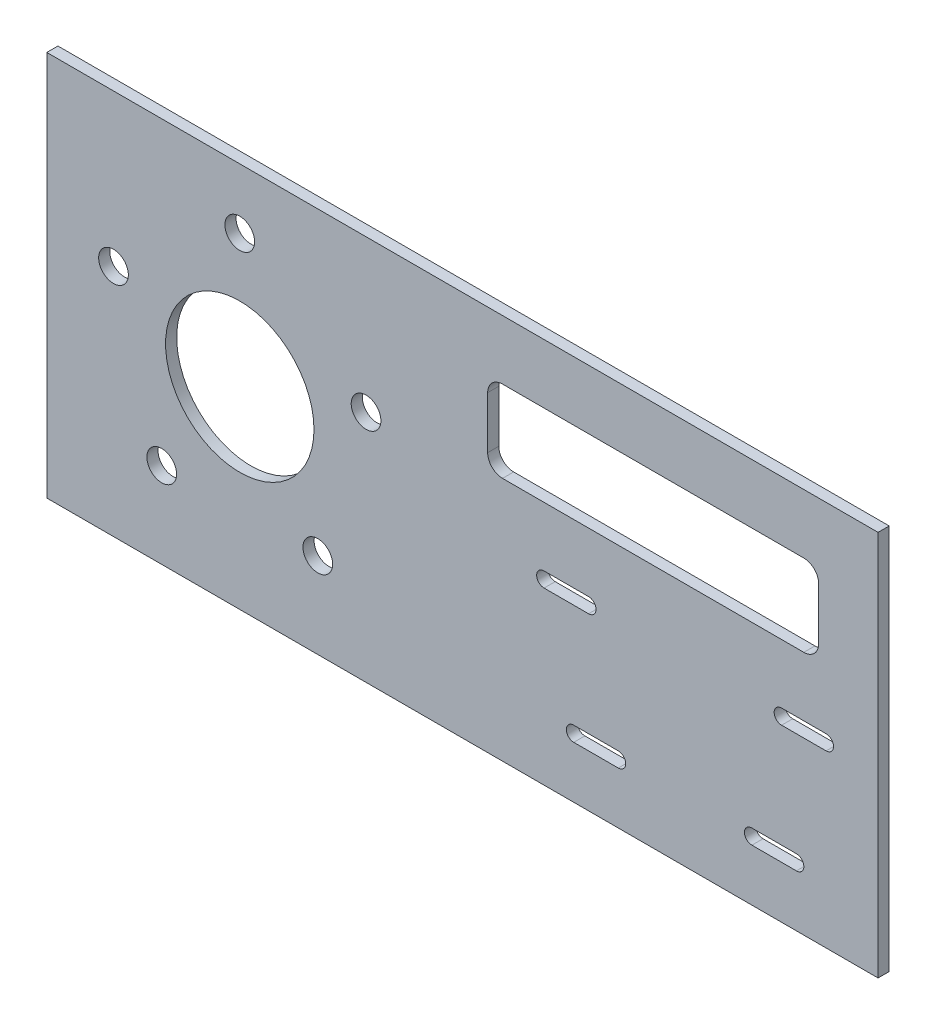
SolidWorks part; units mm, degrees
material "ASTM A36 Steel"
ref_plane "Front Plane" through (0, 0, 0) normal (0, 0, 1) x (1, 0, 0)
ref_plane "Top Plane" through (0, 0, 0) normal (0, 1, 0) x (1, 0, 0)
ref_plane "Right Plane" through (0, 0, 0) normal (1, 0, 0) x (0, 0, -1)
ref_plane "Plane1" through (190.5, 0, 0) normal (1, 0, 0) x (0, 0, -1)
sketch "Sketch1" plane through (0, 0, 0) normal (0, 0, 1) x (1, 0, 0)
  circle A2 centre (0, 0) radius 80.645
  circle A9 centre (-33.3856, -45.9513) radius 6.35
  circle A10 centre (33.3856, -45.9513) radius 6.35
  circle A11 centre (54.019, 17.5518) radius 6.35
  circle A12 centre (0, 56.7989) radius 6.35
  circle A13 centre (-54.019, 17.5518) radius 6.35
sketch "Sketch2" plane through (0, 0, 0) normal (0, 0, 1) x (1, 0, 0)
  line L0 (2.6194, 0) -> (-2.6194, 0) construction
  line L1 (273.05, -82.55) -> (-82.55, -82.55)
  line L2 (273.05, -82.55) -> (273.05, 82.55)
  line L3 (273.05, 82.55) -> (-82.55, 82.55)
  line L4 (-82.55, -82.55) -> (-82.55, 82.55)
  line L5 (273.05, -82.55) -> (-82.55, 82.55) construction
  line L6 (273.05, 82.55) -> (-82.55, -82.55) construction
  line L7 (0, -2.6194) -> (0, 2.6194) construction
  circle A0 centre (0, 0) radius 31.75
  circle A1 centre (-54.019, 17.5518) radius 6.35 construction
  circle A2 centre (0, 56.7989) radius 6.35 construction
  circle A3 centre (54.019, 17.5518) radius 6.35 construction
  circle A4 centre (33.3856, -45.9513) radius 6.35 construction
  circle A5 centre (-33.3856, -45.9513) radius 6.35 construction
  circle A6 centre (-54.019, 17.5518) radius 6.35
  circle A7 centre (0, 56.7989) radius 6.35
  circle A8 centre (54.019, 17.5518) radius 6.35
  circle A9 centre (33.3856, -45.9513) radius 6.35
  circle A10 centre (-33.3856, -45.9513) radius 6.35
  point P18 (95.25, 0)
  dimension "D1" = 63.5
  dimension "D2" = 165.1
  dimension "D3" = 82.55
  dimension "D4" = 355.6
extrude "Boss-Extrude1" add sketch "Sketch2" along normal blind 4.7625
sketch "Sketch3" plane through (0, 0, 4.7625) normal (0, 0, 1) x (1, 0, 0)
  line L0 (190.5, -2.6194) -> (190.5, 2.6194) construction
  line L1 (139.7, -6.35) -> (241.3, -6.35) construction
  line L2 (190.5, -6.35) -> (190.5, -57.15) construction
  line L3 (152.4, -57.15) -> (228.6, -57.15) construction
  line L4 (149.225, -6.35) -> (130.175, -6.35) construction
  line L5 (139.7, -6.35) -> (228.6, -57.15) construction
  line L6 (152.4, -57.15) -> (241.3, -6.35) construction
  line L7 (149.225, -9.525) -> (130.175, -9.525)
  line L8 (149.225, -3.175) -> (130.175, -3.175)
  line L9 (250.825, -6.35) -> (231.775, -6.35) construction
  line L10 (250.825, -9.525) -> (231.775, -9.525)
  line L11 (250.825, -3.175) -> (231.775, -3.175)
  line L12 (238.125, -57.15) -> (219.075, -57.15) construction
  line L13 (238.125, -60.325) -> (219.075, -60.325)
  line L14 (238.125, -53.975) -> (219.075, -53.975)
  line L15 (142.875, -57.15) -> (161.925, -57.15) construction
  line L16 (142.875, -53.975) -> (161.925, -53.975)
  line L17 (142.875, -60.325) -> (161.925, -60.325)
  line L18 (273.05, 82.55) -> (-82.55, 82.55) construction
  arc A0 (149.225, -9.525) -> (149.225, -3.175) centre (149.225, -6.35) ccw
  arc A1 (130.175, -3.175) -> (130.175, -9.525) centre (130.175, -6.35) ccw
  arc A2 (250.825, -9.525) -> (250.825, -3.175) centre (250.825, -6.35) ccw
  arc A3 (231.775, -3.175) -> (231.775, -9.525) centre (231.775, -6.35) ccw
  arc A4 (238.125, -60.325) -> (238.125, -53.975) centre (238.125, -57.15) ccw
  arc A5 (219.075, -53.975) -> (219.075, -60.325) centre (219.075, -57.15) ccw
  arc A6 (142.875, -53.975) -> (142.875, -60.325) centre (142.875, -57.15) ccw
  arc A7 (161.925, -60.325) -> (161.925, -53.975) centre (161.925, -57.15) ccw
  point P0 (190.5, -35.3786)
  point P11 (139.7, -6.35)
  point P18 (241.3, -6.35)
  point P23 (228.6, -57.15)
  point P30 (152.4, -57.15)
  dimension "D1" = 50.8
  dimension "D2" = 101.6
  dimension "D3" = 76.2
  dimension "D4" = 88.9
  dimension "D5" = 19.05
  dimension "D6" = 6.35
extrude "Cut-Extrude1" cut sketch "Sketch3" against normal through all
ref_plane "Plane2" through (0, -6.35, 0) normal (0, 1, 0) x (-1, 0, 0)
sketch "Sketch4" plane through (0, 0, 4.7625) normal (0, 0, 1) x (1, 0, 0)
  line L0 (241.3, 57.15) -> (112.395, 57.15)
  line L1 (106.045, 50.8) -> (106.045, 28.575)
  line L2 (112.395, 22.225) -> (241.3, 22.225)
  line L3 (247.65, 28.575) -> (247.65, 50.8)
  line L4 (273.05, 82.55) -> (-82.55, 82.55) construction
  line L5 (273.05, -82.55) -> (273.05, 82.55) construction
  line L6 (149.225, -3.175) -> (130.175, -3.175) construction
  arc A0 (112.395, 57.15) -> (106.045, 50.8) centre (112.395, 50.8) ccw
  arc A1 (106.045, 28.575) -> (112.395, 22.225) centre (112.395, 28.575) ccw
  arc A2 (241.3, 22.225) -> (247.65, 28.575) centre (241.3, 28.575) ccw
  arc A3 (247.65, 50.8) -> (241.3, 57.15) centre (241.3, 50.8) ccw
  circle A5 centre (0, 0) radius 80.645 construction
  circle A6 centre (0, 0) radius 80.645
  point P21 (80.645, 0)
  dimension "D4" = 6.35
  dimension "D1" = 25.4
  dimension "D2" = 25.4
  dimension "D3" = 25.4
  dimension "D5" = 25.4
extrude "Cut-Extrude3" cut sketch "Sketch4" against normal through all contours L3 A3 L0 A0 L1 A1 L2 A2
